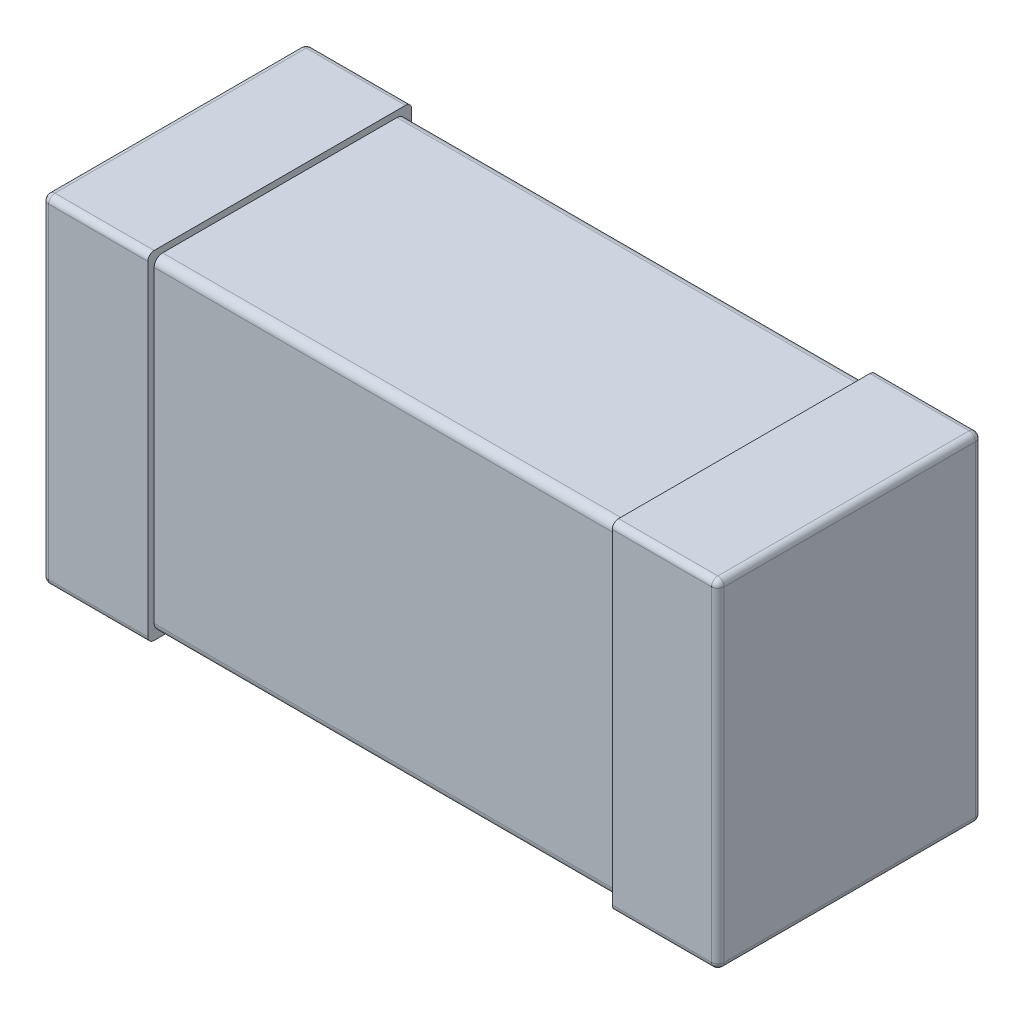
SolidWorks part; units mm, degrees
ref_plane "Спереди" through (0, 0, 0) normal (0, 0, 1) x (1, 0, 0)
ref_plane "Сверху" through (0, 0, 0) normal (0, 1, 0) x (1, 0, 0)
ref_plane "Справа" through (0, 0, 0) normal (1, 0, 0) x (0, 0, -1)
sketch "Эскиз2" plane through (0, 0, 0) normal (0, 0, 1) x (1, 0, 0)
  line L1 (-1.1, 0.77) -> (1.1, 0.77)
  line L2 (-1.1, 0.77) -> (-1.1, -0.77)
  line L3 (-1.1, -0.77) -> (1.1, -0.77)
  line L4 (1.1, 0.77) -> (1.1, -0.77)
  point P0 (0, 0)
extrude "Вытянуть2" add sketch "Эскиз2" along normal blind 1.19 from offset 0.03
sketch "Эскиз3" plane through (0, 0, 0) normal (0, 0, 1) x (1, 0, 0)
  line L1 (1.6, 0.8) -> (1.1, 0.8)
  line L2 (1.6, 0.8) -> (1.6, -0.8)
  line L3 (1.6, -0.8) -> (1.1, -0.8)
  line L4 (1.1, 0.8) -> (1.1, -0.8)
  line L5 (-1.6, 0.8) -> (-1.1, 0.8)
  line L6 (-1.6, 0.8) -> (-1.6, -0.8)
  line L7 (-1.6, -0.8) -> (-1.1, -0.8)
  line L8 (-1.1, 0.8) -> (-1.1, -0.8)
extrude "Вытянуть3" add sketch "Эскиз3" along normal blind 1.25
fillet "Скругление1" radius 0.04 4 edges at (0, 0.77, 0.03) (0, -0.77, 0.03) (0, 0.77, 1.22) (0, -0.77, 1.22)
fillet "Скругление2" radius 0.03 16 edges at (1.6, -0.8, 0.625) (1.6, 0, 1.25) (1.6, 0.8, 0.625) (1.6, 0, 0) (-1.6, 0.8, 0.625) (-1.6, 0, 1.25) (-1.6, -0.8, 0.625) (-1.6, 0, 0) (1.35, 0.8, 0) (-1.35, 0.8, 0) (-1.35, -0.8, 0) (1.35, -0.8, 0) (1.35, 0.8, 1.25) (1.35, -0.8, 1.25) (-1.35, 0.8, 1.25) (-1.35, -0.8, 1.25)
